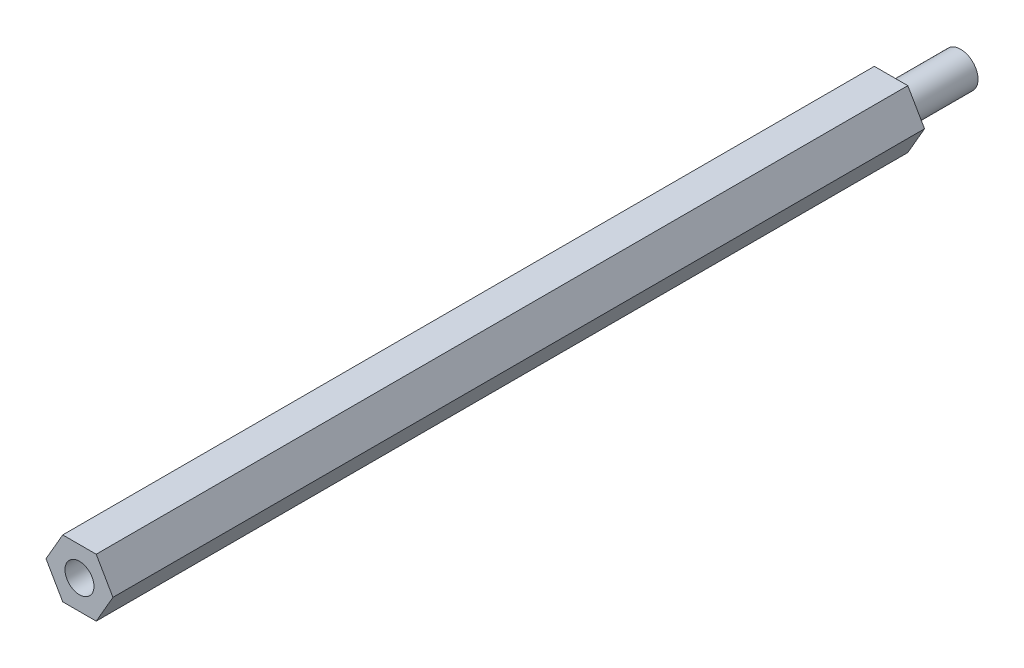
SolidWorks part; units mm, degrees
material "黃銅"
ref_plane "前基準面" through (0, 0, 0) normal (0, 0, 1) x (1, 0, 0)
ref_plane "上基準面" through (0, 0, 0) normal (0, 1, 0) x (1, 0, 0)
ref_plane "右基準面" through (0, 0, 0) normal (1, 0, 0) x (0, 0, -1)
sketch "草圖1" plane through (0, 0, 0) normal (0, 0, 1) x (1, 0, 0)
  line L1 (-1.4434, 2.5) -> (-2.8868, 0)
  line L2 (-2.8868, 0) -> (-1.4434, -2.5)
  line L3 (-1.4434, -2.5) -> (1.4434, -2.5)
  line L4 (1.4434, -2.5) -> (2.8868, 0)
  line L5 (2.8868, 0) -> (1.4434, 2.5)
  line L6 (1.4434, 2.5) -> (-1.4434, 2.5)
  circle A0 centre (0, 0) radius 2.5 construction
  dimension "D1" = 5
extrude "填料-伸長1" add sketch "草圖1" along normal blind 70
sketch "草圖4" plane through (0, 0, 0) normal (0, 0, -1) x (-1, 0, 0)
  circle A0 centre (0, 0) radius 1.5
  dimension "D1" = 3
extrude "填料-伸長2" add sketch "草圖4" along normal blind 6
hole_wizard "M3x0.5 螺紋孔1" positions "草圖2" profile "草圖3" tap size "M3x0.5" standard "Ansi Metric"
sketch "草圖2" plane through (0, 0, 70) normal (0, 0, 1) x (1, 0, 0)
  point P0 (0, 0)
sketch "草圖3" plane through (0, 0, 70) normal (1, 0, 0) x (0, -1, 0)
  line L0 (0, 0) -> (0, 8.2511)
  line L1 (0, 8.2511) -> (1.25, 7.5)
  line L2 (1.25, 7.5) -> (1.25, 0)
  line L5 (1.25, 0) -> (0, 0)
  line L10 (0, 8.2511) -> (-1.25, 7.5) construction
  line L11 (0, -6.35) -> (0, 107.95) construction
  dimension "螺孔鑽直徑" = 2.5
  dimension "螺孔鑽深度" = 7.5
  dimension "導頭角度" = 118
